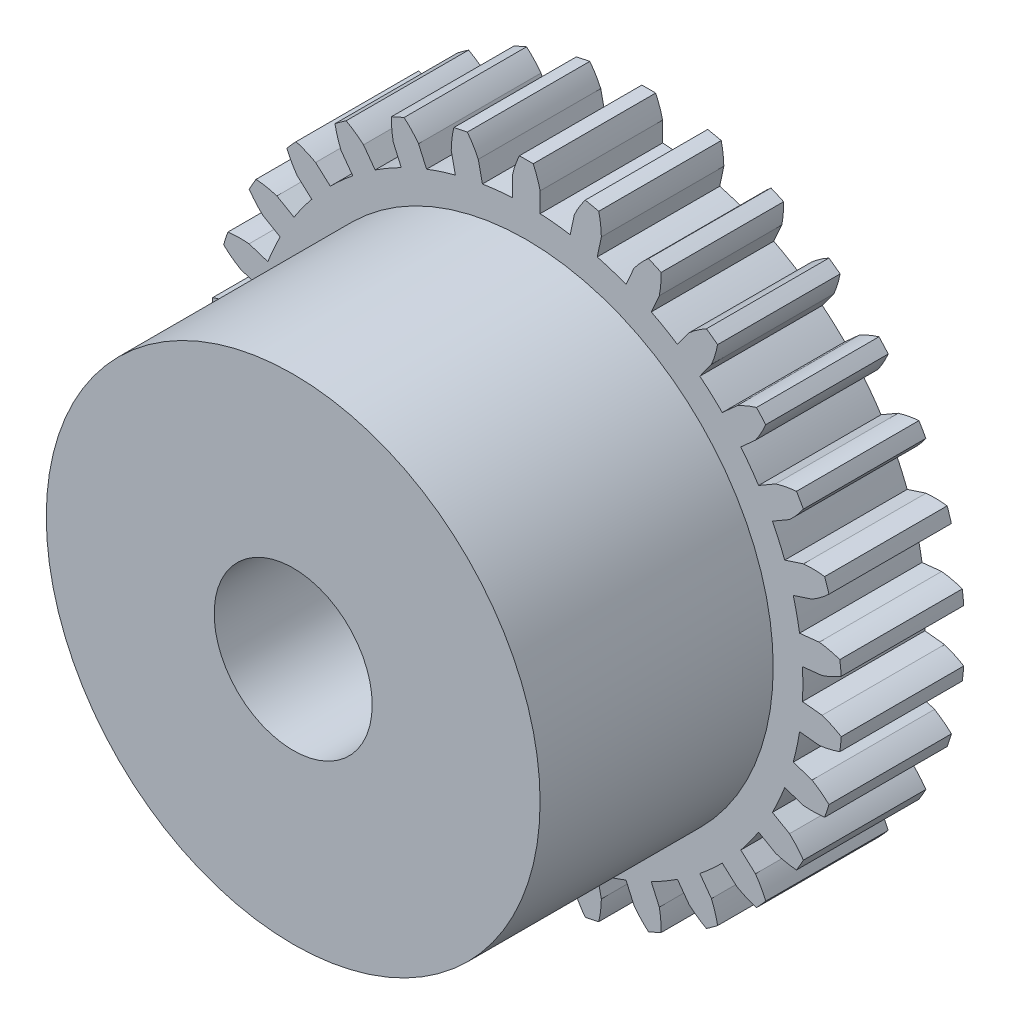
SolidWorks part; units mm, degrees
material "Cast Carbon Steel"
ref_plane "Front Plane" through (0, 0, 0) normal (0, 0, 1) x (1, 0, 0)
ref_plane "Top Plane" through (0, 0, 0) normal (0, 1, 0) x (1, 0, 0)
ref_plane "Right Plane" through (0, 0, 0) normal (1, 0, 0) x (0, 0, -1)
sketch "Sketch1" plane through (0, 0, 0) normal (0, 0, 1) x (1, 0, 0)
  line L50 (2.4303, 14.8006) -> (2.2224, 13.8225)
  line L51 (0, 0) -> (0, 29.8) construction
  line L52 (-0.7, 14.9825) -> (-0.7, 13.9825)
  line L53 (0.7, 14.9825) -> (0.7, 13.9825)
  line L54 (3.7997, 14.5095) -> (3.5918, 13.5314)
  line L55 (5.4544, 13.9719) -> (5.0477, 13.0584)
  line L56 (6.7334, 13.4025) -> (6.3267, 12.4889)
  line L57 (8.2402, 12.5325) -> (7.6524, 11.7235)
  line L58 (9.3728, 11.7096) -> (8.785, 10.9006)
  line L59 (10.6658, 10.5454) -> (9.9226, 9.8763)
  line L60 (11.6026, 9.505) -> (10.8594, 8.8359)
  line L61 (12.6252, 8.0975) -> (11.7592, 7.5975)
  line L62 (13.3252, 6.885) -> (12.4592, 6.385)
  line L63 (14.0329, 5.2956) -> (13.0818, 4.9866)
  line L64 (14.4655, 3.9641) -> (13.5144, 3.6551)
  line L65 (14.8272, 2.2623) -> (13.8327, 2.1577)
  line L66 (14.9736, 0.8699) -> (13.9791, 0.7654)
  line L67 (14.9736, -0.8699) -> (13.9791, -0.7654)
  line L68 (14.8272, -2.2623) -> (13.8327, -2.1577)
  line L69 (14.4655, -3.9641) -> (13.5144, -3.6551)
  line L70 (14.0329, -5.2956) -> (13.0818, -4.9866)
  line L71 (13.3252, -6.885) -> (12.4592, -6.385)
  line L72 (12.6252, -8.0975) -> (11.7592, -7.5975)
  line L73 (11.6026, -9.505) -> (10.8594, -8.8359)
  line L74 (10.6658, -10.5454) -> (9.9226, -9.8763)
  line L75 (9.3728, -11.7096) -> (8.785, -10.9006)
  line L76 (8.2402, -12.5325) -> (7.6524, -11.7235)
  line L77 (6.7334, -13.4025) -> (6.3267, -12.4889)
  line L78 (5.4544, -13.9719) -> (5.0477, -13.0584)
  line L79 (3.7997, -14.5095) -> (3.5918, -13.5314)
  line L80 (2.4303, -14.8006) -> (2.2224, -13.8225)
  line L81 (0.7, -14.9825) -> (0.7, -13.9825)
  line L82 (-0.7, -14.9825) -> (-0.7, -13.9825)
  line L83 (-2.4303, -14.8006) -> (-2.2224, -13.8225)
  line L84 (-3.7997, -14.5095) -> (-3.5918, -13.5314)
  line L85 (-5.4544, -13.9719) -> (-5.0477, -13.0584)
  line L86 (-6.7334, -13.4025) -> (-6.3267, -12.4889)
  line L87 (-8.2402, -12.5325) -> (-7.6524, -11.7235)
  line L88 (-9.3728, -11.7096) -> (-8.785, -10.9006)
  line L89 (-10.6658, -10.5454) -> (-9.9226, -9.8763)
  line L90 (-11.6026, -9.505) -> (-10.8594, -8.8359)
  line L91 (-12.6252, -8.0975) -> (-11.7592, -7.5975)
  line L92 (-13.3252, -6.885) -> (-12.4592, -6.385)
  line L93 (-14.0329, -5.2956) -> (-13.0818, -4.9866)
  line L94 (-14.4655, -3.9641) -> (-13.5144, -3.6551)
  line L95 (-14.8272, -2.2623) -> (-13.8327, -2.1577)
  line L96 (-14.9736, -0.8699) -> (-13.9791, -0.7654)
  line L97 (-14.9736, 0.8699) -> (-13.9791, 0.7654)
  line L98 (-14.8272, 2.2623) -> (-13.8327, 2.1577)
  line L99 (-14.4655, 3.9641) -> (-13.5144, 3.6551)
  line L100 (-14.0329, 5.2956) -> (-13.0818, 4.9866)
  line L101 (-13.3252, 6.885) -> (-12.4592, 6.385)
  line L102 (-12.6252, 8.0975) -> (-11.7592, 7.5975)
  line L103 (-11.6026, 9.505) -> (-10.8594, 8.8359)
  line L104 (-10.6658, 10.5454) -> (-9.9226, 9.8763)
  line L105 (-9.3728, 11.7096) -> (-8.785, 10.9006)
  line L106 (-8.2402, 12.5325) -> (-7.6524, 11.7235)
  line L107 (-6.7334, 13.4025) -> (-6.3267, 12.4889)
  line L108 (-5.4544, 13.9719) -> (-5.0477, 13.0584)
  line L109 (-3.7997, 14.5095) -> (-3.5918, 13.5314)
  line L110 (-2.4303, 14.8006) -> (-2.2224, 13.8225)
  arc A58 (-0.35, 15.9962) -> (-0.7, 14.9825) centre (4.111, 13.8886) ccw
  arc A59 (0.35, 15.9962) -> (0.7, 14.9825) centre (-4.111, 13.8886) cw
  circle A61 centre (0, 0) radius 15 construction
  arc A63 (0.35, 15.9962) -> (-0.35, 15.9962) centre (0, 0) ccw
  arc A64 (2.9834, 15.7194) -> (2.4303, 14.8006) centre (6.9087, 12.7304) ccw
  arc A65 (3.6681, 15.5738) -> (3.7997, 14.5095) centre (-1.1335, 14.4399) cw
  arc A66 (3.6681, 15.5738) -> (2.9834, 15.7194) centre (0, 0) ccw
  arc A67 (6.1865, 14.7556) -> (5.4544, 13.9719) centre (9.4046, 11.0158) ccw
  arc A68 (6.826, 14.4709) -> (6.7334, 13.4025) centre (1.8935, 14.36) cw
  arc A69 (6.826, 14.4709) -> (6.1865, 14.7556) centre (0, 0) ccw
  arc A70 (9.1192, 13.1469) -> (8.2402, 12.5325) centre (11.4894, 8.8198) ccw
  arc A71 (9.6855, 12.7354) -> (9.3728, 11.7096) centre (4.8377, 13.6525) cw
  arc A72 (9.6855, 12.7354) -> (9.1192, 13.1469) centre (0, 0) ccw
  arc A73 (11.6533, 10.9636) -> (10.6658, 10.5454) centre (13.072, 6.2383) ccw
  arc A74 (12.1217, 10.4434) -> (11.6026, 9.505) centre (7.5705, 12.3484) cw
  arc A75 (12.1217, 10.4434) -> (11.6533, 10.9636) centre (0, 0) ccw
  arc A76 (13.6781, 8.3012) -> (12.6252, 8.0975) centre (14.0834, 3.3841) ccw
  arc A77 (14.0281, 7.695) -> (13.3252, 6.885) centre (9.9724, 10.5045) cw
  arc A78 (14.0281, 7.695) -> (13.6781, 8.3012) centre (0, 0) ccw
  arc A79 (15.1051, 5.276) -> (14.0329, 5.2956) centre (14.4792, 0.3821) ccw
  arc A80 (15.3214, 4.6102) -> (14.4655, 3.9641) centre (11.9385, 8.2016) cw
  arc A81 (15.3214, 4.6102) -> (15.1051, 5.276) centre (0, 0) ccw
  arc A82 (15.872, 2.0201) -> (14.8272, 2.2623) centre (14.2423, -2.6367) ccw
  arc A83 (15.9451, 1.324) -> (14.9736, 0.8699) centre (13.3828, 5.5402) cw
  arc A84 (15.9451, 1.324) -> (15.872, 2.0201) centre (0, 0) ccw
  arc A85 (15.9451, -1.324) -> (14.9736, -0.8699) centre (13.3828, -5.5402) ccw
  arc A86 (15.872, -2.0201) -> (14.8272, -2.2623) centre (14.2423, 2.6367) cw
  arc A87 (15.872, -2.0201) -> (15.9451, -1.324) centre (0, 0) ccw
  arc A88 (15.3214, -4.6102) -> (14.4655, -3.9641) centre (11.9385, -8.2016) ccw
  arc A89 (15.1051, -5.276) -> (14.0329, -5.2956) centre (14.4792, -0.3821) cw
  arc A90 (15.1051, -5.276) -> (15.3214, -4.6102) centre (0, 0) ccw
  arc A91 (14.0281, -7.695) -> (13.3252, -6.885) centre (9.9724, -10.5045) ccw
  arc A92 (13.6781, -8.3012) -> (12.6252, -8.0975) centre (14.0834, -3.3841) cw
  arc A93 (13.6781, -8.3012) -> (14.0281, -7.695) centre (0, 0) ccw
  arc A94 (12.1217, -10.4434) -> (11.6026, -9.505) centre (7.5705, -12.3484) ccw
  arc A95 (11.6533, -10.9636) -> (10.6658, -10.5454) centre (13.072, -6.2383) cw
  arc A96 (11.6533, -10.9636) -> (12.1217, -10.4434) centre (0, 0) ccw
  arc A97 (9.6855, -12.7354) -> (9.3728, -11.7096) centre (4.8377, -13.6525) ccw
  arc A98 (9.1192, -13.1469) -> (8.2402, -12.5325) centre (11.4894, -8.8198) cw
  arc A99 (9.1192, -13.1469) -> (9.6855, -12.7354) centre (0, 0) ccw
  arc A100 (6.826, -14.4709) -> (6.7334, -13.4025) centre (1.8935, -14.36) ccw
  arc A101 (6.1865, -14.7556) -> (5.4544, -13.9719) centre (9.4046, -11.0158) cw
  arc A102 (6.1865, -14.7556) -> (6.826, -14.4709) centre (0, 0) ccw
  arc A103 (3.6681, -15.5738) -> (3.7997, -14.5095) centre (-1.1335, -14.4399) ccw
  arc A104 (2.9834, -15.7194) -> (2.4303, -14.8006) centre (6.9087, -12.7304) cw
  arc A105 (2.9834, -15.7194) -> (3.6681, -15.5738) centre (0, 0) ccw
  arc A106 (0.35, -15.9962) -> (0.7, -14.9825) centre (-4.111, -13.8886) ccw
  arc A107 (-0.35, -15.9962) -> (-0.7, -14.9825) centre (4.111, -13.8886) cw
  arc A108 (-0.35, -15.9962) -> (0.35, -15.9962) centre (0, 0) ccw
  arc A109 (-2.9834, -15.7194) -> (-2.4303, -14.8006) centre (-6.9087, -12.7304) ccw
  arc A110 (-3.6681, -15.5738) -> (-3.7997, -14.5095) centre (1.1335, -14.4399) cw
  arc A111 (-3.6681, -15.5738) -> (-2.9834, -15.7194) centre (0, 0) ccw
  arc A112 (-6.1865, -14.7556) -> (-5.4544, -13.9719) centre (-9.4046, -11.0158) ccw
  arc A113 (-6.826, -14.4709) -> (-6.7334, -13.4025) centre (-1.8935, -14.36) cw
  arc A114 (-6.826, -14.4709) -> (-6.1865, -14.7556) centre (0, 0) ccw
  arc A115 (-9.1192, -13.1469) -> (-8.2402, -12.5325) centre (-11.4894, -8.8198) ccw
  arc A116 (-9.6855, -12.7354) -> (-9.3728, -11.7096) centre (-4.8377, -13.6525) cw
  circle A117 centre (0, 0) radius 14
  arc A118 (-9.6855, -12.7354) -> (-9.1192, -13.1469) centre (0, 0) ccw
  arc A119 (-11.6533, -10.9636) -> (-10.6658, -10.5454) centre (-13.072, -6.2383) ccw
  arc A120 (-12.1217, -10.4434) -> (-11.6026, -9.505) centre (-7.5705, -12.3484) cw
  arc A121 (-12.1217, -10.4434) -> (-11.6533, -10.9636) centre (0, 0) ccw
  arc A122 (-13.6781, -8.3012) -> (-12.6252, -8.0975) centre (-14.0834, -3.3841) ccw
  arc A123 (-14.0281, -7.695) -> (-13.3252, -6.885) centre (-9.9724, -10.5045) cw
  arc A124 (-14.0281, -7.695) -> (-13.6781, -8.3012) centre (0, 0) ccw
  arc A125 (-15.1051, -5.276) -> (-14.0329, -5.2956) centre (-14.4792, -0.3821) ccw
  arc A126 (-15.3214, -4.6102) -> (-14.4655, -3.9641) centre (-11.9385, -8.2016) cw
  arc A127 (-15.3214, -4.6102) -> (-15.1051, -5.276) centre (0, 0) ccw
  arc A128 (-15.872, -2.0201) -> (-14.8272, -2.2623) centre (-14.2423, 2.6367) ccw
  arc A129 (-15.9451, -1.324) -> (-14.9736, -0.8699) centre (-13.3828, -5.5402) cw
  arc A130 (-15.9451, -1.324) -> (-15.872, -2.0201) centre (0, 0) ccw
  arc A131 (-15.9451, 1.324) -> (-14.9736, 0.8699) centre (-13.3828, 5.5402) ccw
  arc A132 (-15.872, 2.0201) -> (-14.8272, 2.2623) centre (-14.2423, -2.6367) cw
  arc A133 (-15.872, 2.0201) -> (-15.9451, 1.324) centre (0, 0) ccw
  arc A134 (-15.3214, 4.6102) -> (-14.4655, 3.9641) centre (-11.9385, 8.2016) ccw
  arc A135 (-15.1051, 5.276) -> (-14.0329, 5.2956) centre (-14.4792, 0.3821) cw
  arc A136 (-15.1051, 5.276) -> (-15.3214, 4.6102) centre (0, 0) ccw
  arc A137 (-14.0281, 7.695) -> (-13.3252, 6.885) centre (-9.9724, 10.5045) ccw
  arc A138 (-13.6781, 8.3012) -> (-12.6252, 8.0975) centre (-14.0834, 3.3841) cw
  arc A139 (-13.6781, 8.3012) -> (-14.0281, 7.695) centre (0, 0) ccw
  arc A140 (-12.1217, 10.4434) -> (-11.6026, 9.505) centre (-7.5705, 12.3484) ccw
  arc A141 (-11.6533, 10.9636) -> (-10.6658, 10.5454) centre (-13.072, 6.2383) cw
  arc A142 (-11.6533, 10.9636) -> (-12.1217, 10.4434) centre (0, 0) ccw
  arc A143 (-9.6855, 12.7354) -> (-9.3728, 11.7096) centre (-4.8377, 13.6525) ccw
  arc A144 (-9.1192, 13.1469) -> (-8.2402, 12.5325) centre (-11.4894, 8.8198) cw
  arc A145 (-9.1192, 13.1469) -> (-9.6855, 12.7354) centre (0, 0) ccw
  arc A146 (-6.826, 14.4709) -> (-6.7334, 13.4025) centre (-1.8935, 14.36) ccw
  arc A147 (-6.1865, 14.7556) -> (-5.4544, 13.9719) centre (-9.4046, 11.0158) cw
  arc A148 (-6.1865, 14.7556) -> (-6.826, 14.4709) centre (0, 0) ccw
  arc A149 (-3.6681, 15.5738) -> (-3.7997, 14.5095) centre (1.1335, 14.4399) ccw
  arc A150 (-2.9834, 15.7194) -> (-2.4303, 14.8006) centre (-6.9087, 12.7304) cw
  arc A151 (-2.9834, 15.7194) -> (-3.6681, 15.5738) centre (0, 0) ccw
  point P183 (0, 0)
  point P208 (0, 0)
  dimension "D1" = 32
  dimension "D2" = 30
  dimension "D3" = 28
  dimension "D4" = 1
  dimension "D5" = 0.35
  dimension "D6" = 30
  dimension "D7" = 0.7
extrude "Boss-Extrude1" add sketch "Sketch1" along normal blind 6.2
sketch "Sketch2" plane through (0, 0, 6.2) normal (0, 0, 1) x (1, 0, 0)
  circle A0 centre (0, 0) radius 12.5
  dimension "D1" = 25
extrude "Boss-Extrude2" add sketch "Sketch2" along normal blind 11.8
sketch "Sketch3" plane through (0, 0, 18) normal (0, 0, 1) x (1, 0, 0)
  circle A0 centre (0, 0) radius 4
  dimension "D1" = 8
extrude "Cut-Extrude1" cut sketch "Sketch3" against normal up to next
sketch "Sketch4" plane through (0, 0, 0) normal (0, 1, 0) x (1, 0, 0)
  line L0 (0.35, -6.2) -> (0.7, -6.2) construction
  circle A0 centre (0, -9.7) radius 1.25
  point P4 (0.525, -6.2)
  dimension "D1" = 2.5
  dimension "D2" = 3.5
extrude "Cut-Extrude2" cut sketch "Sketch4" against normal up to surface (12.5 mm away)
